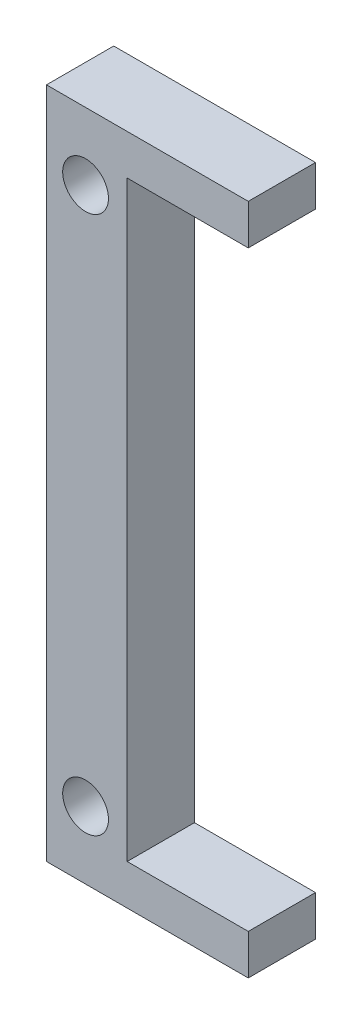
SolidWorks part; units mm, degrees
ref_plane "Front Plane" through (0, 0, 0) normal (0, 0, 1) x (1, 0, 0)
ref_plane "Top Plane" through (0, 0, 0) normal (0, 1, 0) x (1, 0, 0)
ref_plane "Right Plane" through (0, 0, 0) normal (1, 0, 0) x (0, 0, -1)
sketch "Sketch1" plane through (0, 0, 0) normal (0, 0, 1) x (1, 0, 0)
  line L0 (8.2353, 18.8824) -> (-6.7647, 18.8824)
  line L2 (-6.7647, 14.2941) -> (-6.7647, -31.1176)
  line L3 (-6.7647, -31.1176) -> (-0.8824, -31.1176)
  line L4 (-0.7647, 15.8824) -> (-0.7647, -28.1176)
  line L7 (-0.7647, 15.8824) -> (8.2353, 15.8824)
  line L8 (8.2353, 18.8824) -> (8.2353, 15.8824)
  line L9 (-6.7647, -31.1176) -> (8.2353, -31.1176)
  line L10 (-6.7647, -31.1176) -> (-6.7647, -25.3529)
  line L11 (-0.7647, -28.1176) -> (8.2353, -28.1176)
  line L12 (8.2353, -31.1176) -> (8.2353, -28.1176)
  line L13 (-6.7647, 18.8824) -> (-6.7647, 14.2941)
  dimension "D1" = 50
  dimension "D2" = 3
  dimension "D3" = 3
  dimension "D4" = 6
  dimension "D5" = 15
  dimension "D6" = 15
extrude "Boss-Extrude1" add sketch "Sketch1" along normal blind 5 contours L0 L13 L2 L3 L9 L12 L11 L4 L7 L8
hole_wizard "M3 Clearance Hole2" positions "Sketch4" profile "Sketch5" hole size "M3" standard "ISO" end condition through all
sketch "Sketch4" plane through (0, 0, 5) normal (0, 0, 1) x (1, 0, 0)
  line L0 (8.2353, 18.8824) -> (-6.7647, 18.8824) construction
  line L1 (-6.7647, -31.1176) -> (8.2353, -31.1176) construction
  point P0 (-3.8589, 13.8824)
  point P2 (-3.8589, -26.1176)
  dimension "D1" = 5
  dimension "D2" = 5
sketch "Sketch5" plane through (-3.8589, 13.8824, 5) normal (1, 0, 0) x (0, -1, 0)
  line L0 (0, 0) -> (0, 5)
  line L1 (0, 5) -> (1.7, 5)
  line L2 (1.7, 5) -> (1.7, 0)
  line L5 (1.7, 0) -> (0, 0)
  line L11 (0, -6.35) -> (0, 107.95) construction
  dimension "Thru Hole Dia." = 3.4
  dimension "Thru Hole Depth" = 5
